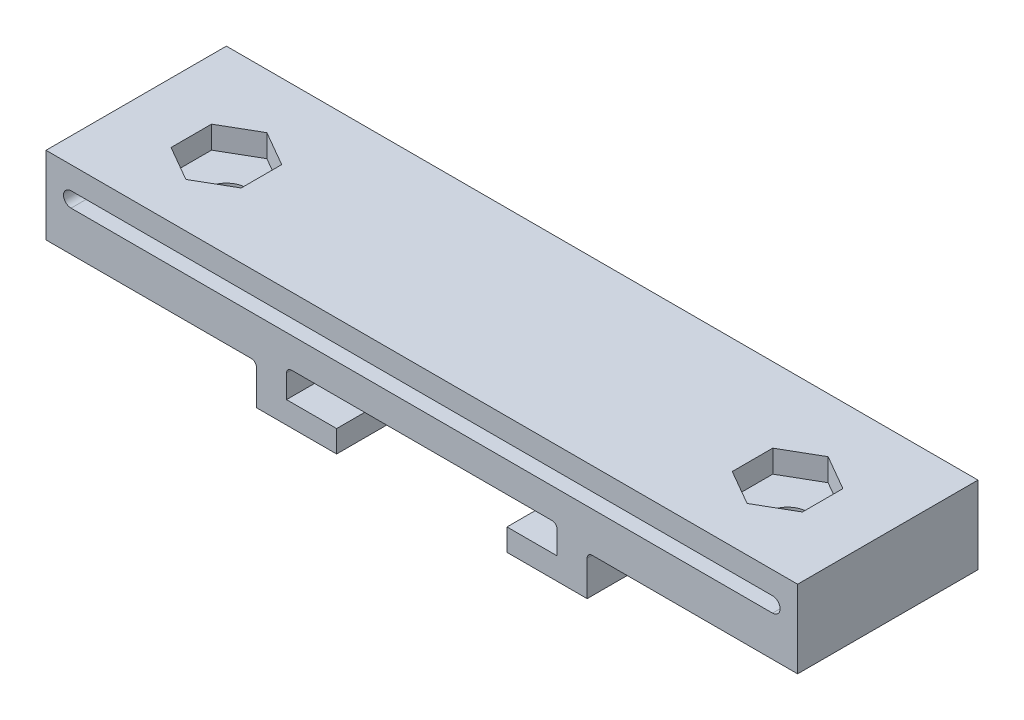
SolidWorks part; units mm, degrees
ref_plane "Płaszczyzna przednia" through (0, 0, 0) normal (0, 0, 1) x (1, 0, 0)
ref_plane "Płaszczyzna górna" through (0, 0, 0) normal (0, 1, 0) x (1, 0, 0)
ref_plane "Płaszczyzna prawa" through (0, 0, 0) normal (1, 0, 0) x (0, 0, -1)
sketch "Szkic1" plane through (0, 0, 0) normal (0, 0, 1) x (1, 0, 0)
  line L0 (-13, 4.2) -> (-13, 6) construction
  line L1 (-13, 6) -> (13, 6) construction
  line L2 (13, 6) -> (13, 4.2) construction
  line L3 (13, 4.2) -> (8, 4.2) construction
  line L4 (8, 4.2) -> (8, 0) construction
  line L5 (8, 0) -> (-8, 0) construction
  line L6 (-8, 0) -> (-8, 4.2) construction
  line L7 (-8, 4.2) -> (-13, 4.2) construction
  line L8 (0, 0) -> (0, 20.9107) construction
  line L9 (-13.5, 3.7) -> (-13.5, 6.5)
  line L10 (-13.5, 6.5) -> (13.5, 6.5)
  line L11 (13.5, 6.5) -> (13.5, 3.7)
  line L12 (13.5, 3.7) -> (8.5, 3.7)
  line L13 (8.5, 3.7) -> (8.5, 1.5)
  line L14 (-8.5, 1.5) -> (-16.5, 1.5)
  line L15 (-8.5, 1.5) -> (-8.5, 3.7)
  line L16 (-8.5, 3.7) -> (-13.5, 3.7)
  line L17 (8.5, -0.5) -> (-8.5, -0.5) construction
  line L18 (8.5, 3.7) -> (8.5, -0.5) construction
  line L19 (-8.5, -0.5) -> (-8.5, 3.7) construction
  line L20 (-16.5, 1.5) -> (-16.5, 5.5)
  line L21 (-16.5, 5.5) -> (-35, 5.5)
  line L22 (-35, 5.5) -> (-35, 9.5)
  line L23 (-35, 9.5) -> (35, 9.5)
  line L24 (35, 9.5) -> (35, 5.5)
  line L25 (35, 5.5) -> (16.5, 5.5)
  line L26 (16.5, 5.5) -> (16.5, 1.5)
  line L27 (16.5, 1.5) -> (8.5, 1.5)
  point P10 (-10.5, 4.2)
  dimension "D1" = 26
  dimension "D2" = 16
  dimension "D3" = 6
  dimension "D4" = 1.8
  dimension "D6" = 2.2
  dimension "D7" = 3
  dimension "D8" = 4
  dimension "D9" = 3
  dimension "D10" = 70
  dimension "D5" = 0.5
extrude "Dodanie-wyciągnięcie1" add sketch "Szkic1" along normal blind 18
sketch "Szkic4" plane through (0, 9.5, 0) normal (0, 1, 0) x (1, 0, 0)
  line L0 (0, 0) -> (0, -41.373) construction
  line L1 (35, 0) -> (-35, 0) construction
  line L2 (35, -18) -> (-35, -18) construction
  circle A0 centre (-28, -9.5) radius 5
  circle A2 centre (28, -9.5) radius 5
  dimension "D1" = 28
  dimension "D2" = 10
  dimension "D3" = 8.5
extrude "Wytnij-wyciągnięcie1" cut sketch "Szkic4" along normal blind 2 from offset 4 offset against normal yes
sketch "Szkic5" plane through (0, 7.5, 0) normal (0, -1, 0) x (-1, 0, 0)
  circle A0 centre (28, -9.5) radius 5 construction
  circle A1 centre (28, -9.5) radius 2
  circle A3 centre (-28, -9.5) radius 2
  dimension "D3" = 4
  dimension "D4" = 4
extrude "Wytnij-wyciągnięcie2" cut sketch "Szkic5" against normal blind 2.6534
fillet "Zaokrąglenie1" radius 0.5 4 edges at (-13.5, 6.5, 9) (13.5, 6.5, 9) (16.5, 5.5, 9) (-16.5, 5.5, 9)
sketch "Szkic6" plane through (0, 0, 18) normal (0, 0, 1) x (1, 0, 0)
  line L1 (-35, 9.5) -> (-35, 5.5) construction
  line L2 (35, 11) -> (-35, 11)
  line L3 (35, 11) -> (-35, 11)
  line L4 (35, 5.5) -> (35, 9.5) construction
  line L5 (-35, 9.5) -> (-35, 5.5)
  line L6 (35, 5.5) -> (35, 9.5)
  line L7 (-35, 5.5) -> (-37.5, 5.5)
  line L8 (-37.5, 5.5) -> (-37.5, 13.25)
  line L9 (-37.5, 13.25) -> (37.5, 13.25)
  line L10 (37.5, 13.25) -> (37.5, 5.5)
  line L11 (37.5, 5.5) -> (35, 5.5)
  arc A0 (35, 11) -> (35, 9.5) centre (35, 10.25) cw
  arc A1 (-35, 9.5) -> (-35, 11) centre (-35, 10.25) cw
  dimension "D2" = 3
  dimension "D3" = 2.5
  dimension "D4" = 2.5
  dimension "D1" = 1.5
extrude "Dodanie-wyciągnięcie2" add sketch "Szkic6" against normal up to surface (18 mm away) up to face at (0, 4.8607, 0)
sketch "Szkic7" plane through (0, 13.25, 0) normal (0, 1, 0) x (1, 0, 0)
  line L0 (-37.5, 0) -> (-37.5, -18) construction
  line L1 (-31.5, -7.4793) -> (-31.5, -11.5207)
  line L2 (-31.5, -11.5207) -> (-28, -13.5415)
  line L3 (-28, -13.5415) -> (-24.5, -11.5207)
  line L4 (-24.5, -11.5207) -> (-24.5, -7.4793)
  line L5 (-24.5, -7.4793) -> (-28, -5.4585)
  line L6 (-28, -5.4585) -> (-31.5, -7.4793)
  line L7 (28, -5.4585) -> (24.5, -7.4793)
  line L8 (24.5, -7.4793) -> (24.5, -11.5207)
  line L9 (24.5, -11.5207) -> (28, -13.5415)
  line L10 (28, -13.5415) -> (31.5, -11.5207)
  line L11 (31.5, -11.5207) -> (31.5, -7.4793)
  line L12 (31.5, -7.4793) -> (28, -5.4585)
  line L13 (37.5, 0) -> (37.5, -18) construction
  circle A0 centre (-28, -9.5) radius 3.5 construction
  circle A1 centre (28, -9.5) radius 3.5 construction
  dimension "D1" = 7
  dimension "D2" = 7
extrude "Wytnij-wyciągnięcie3" cut sketch "Szkic7" against normal up to next
chamfer "Sfazowanie1" distance 1.5 angle 45 9 edges at (8.5, 2.6, 0) (-8.5, 2.6, 0) (-11, 3.7, 0) (-13.5, 4.85, 0) (-13.3536, 6.3536, 0) (0, 6.5, 0) (13.3536, 6.3536, 0) (11, 3.7, 0) (13.5, 4.85, 0)
equation "\"x\"=4"
equation "\"s\"=10"
